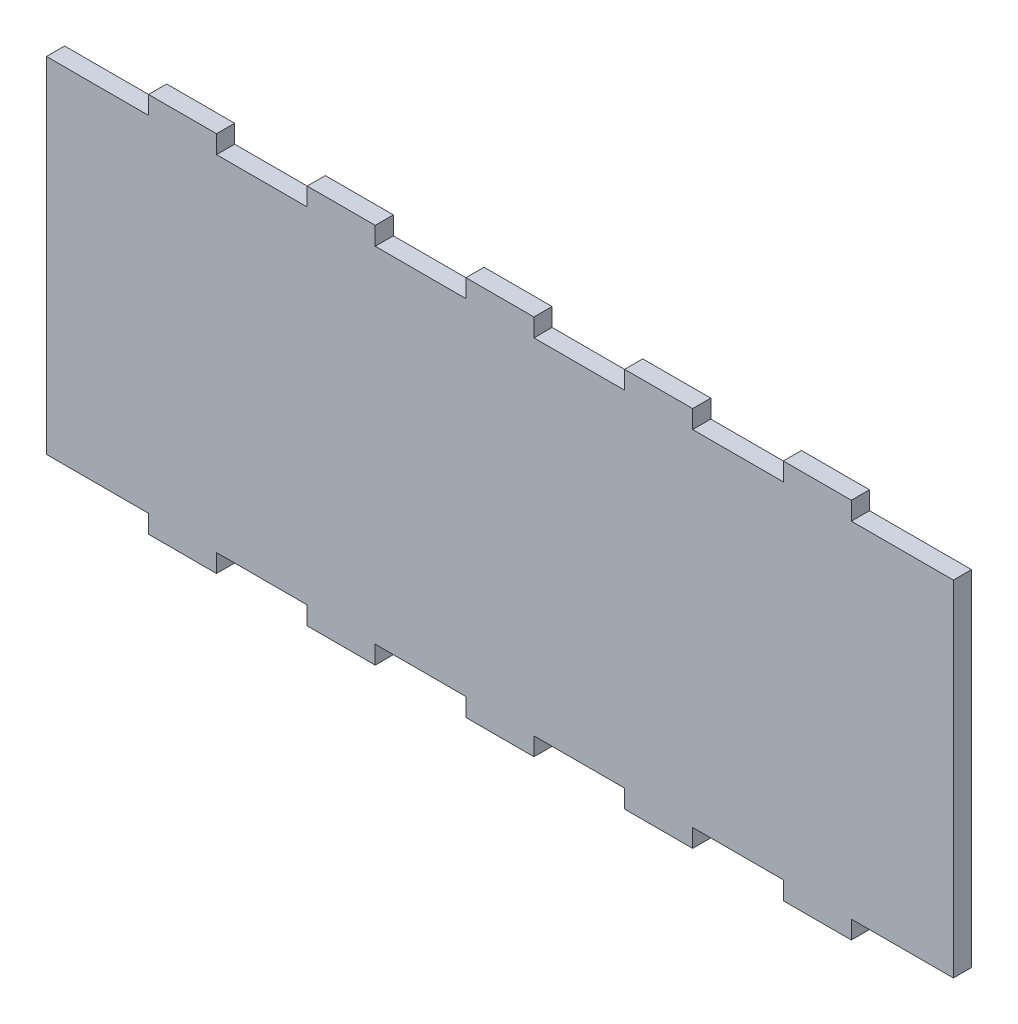
SolidWorks part; units mm, degrees
material "1060 Alloy"
ref_plane "Front Plane" through (0, 0, 0) normal (0, 0, 1) x (1, 0, 0)
ref_plane "Top Plane" through (0, 0, 0) normal (0, 1, 0) x (1, 0, 0)
ref_plane "Right Plane" through (0, 0, 0) normal (1, 0, 0) x (0, 0, -1)
sketch "Sketch2" plane through (0, 0, 0) normal (0, 0, 1) x (1, 0, 0)
  line L0 (37.5, -76) -> (57.5, -76)
  line L1 (0, 0) -> (22.5, 0)
  line L2 (0, 0) -> (0, -76)
  line L3 (0, -76) -> (22.5, -76)
  line L4 (200, 0) -> (200, -76)
  line L5 (0, -38) -> (200, -38) construction
  line L6 (22.5, -76) -> (22.5, -80)
  line L7 (22.5, -80) -> (37.5, -80)
  line L8 (37.5, -76) -> (37.5, -80)
  line L9 (127.5, 4) -> (127.5, 0)
  line L10 (57.5, -76) -> (57.5, -80)
  line L11 (57.5, -80) -> (72.5, -80)
  line L12 (72.5, -76) -> (72.5, -80)
  line L13 (127.5, 4) -> (142.5, 4)
  line L14 (92.5, -76) -> (92.5, -80)
  line L15 (92.5, -80) -> (107.5, -80)
  line L16 (107.5, -76) -> (107.5, -80)
  line L17 (142.5, 4) -> (142.5, 0)
  line L18 (127.5, -76) -> (127.5, -80)
  line L19 (127.5, -80) -> (142.5, -80)
  line L20 (142.5, -76) -> (142.5, -80)
  line L21 (142.5, 0) -> (162.5, 0)
  line L22 (162.5, -76) -> (162.5, -80)
  line L23 (162.5, -80) -> (177.5, -80)
  line L24 (177.5, -76) -> (177.5, -80)
  line L25 (72.5, -76) -> (92.5, -76)
  line L26 (107.5, -76) -> (127.5, -76)
  line L27 (142.5, -76) -> (162.5, -76)
  line L28 (177.5, -76) -> (200, -76)
  line L29 (162.5, 0) -> (162.5, 4)
  line L30 (127.5, 0) -> (107.5, 0)
  line L31 (107.5, 0) -> (107.5, 4)
  line L32 (162.5, 4) -> (177.5, 4)
  line L33 (177.5, 4) -> (177.5, 0)
  line L34 (107.5, 4) -> (92.5, 4)
  line L35 (92.5, 4) -> (92.5, 0)
  line L36 (92.5, 0) -> (72.5, 0)
  line L37 (72.5, 0) -> (72.5, 4)
  line L38 (72.5, 4) -> (57.5, 4)
  line L39 (57.5, 4) -> (57.5, 0)
  line L40 (57.5, 0) -> (37.5, 0)
  line L41 (37.5, 0) -> (37.5, 4)
  line L42 (37.5, 4) -> (22.5, 4)
  line L43 (22.5, 4) -> (22.5, 0)
  line L52 (177.5, 0) -> (200, 0)
  dimension "D1" = 76
  dimension "D2" = 200
  dimension "D3" = 22.5
  dimension "D4" = 22.5
  dimension "D5" = 20
  dimension "D6" = 20
  dimension "D7" = 20
  dimension "D8" = 35
  dimension "D9" = 4
  dimension "D10" = 4
  dimension "D11" = 4
  dimension "D12" = 4
  dimension "D13" = 4
  dimension "D14" = 15
  dimension "D15" = 15
  dimension "D16" = 15
  dimension "D17" = 15
extrude "Boss-Extrude1" add sketch "Sketch2" along normal blind 4
